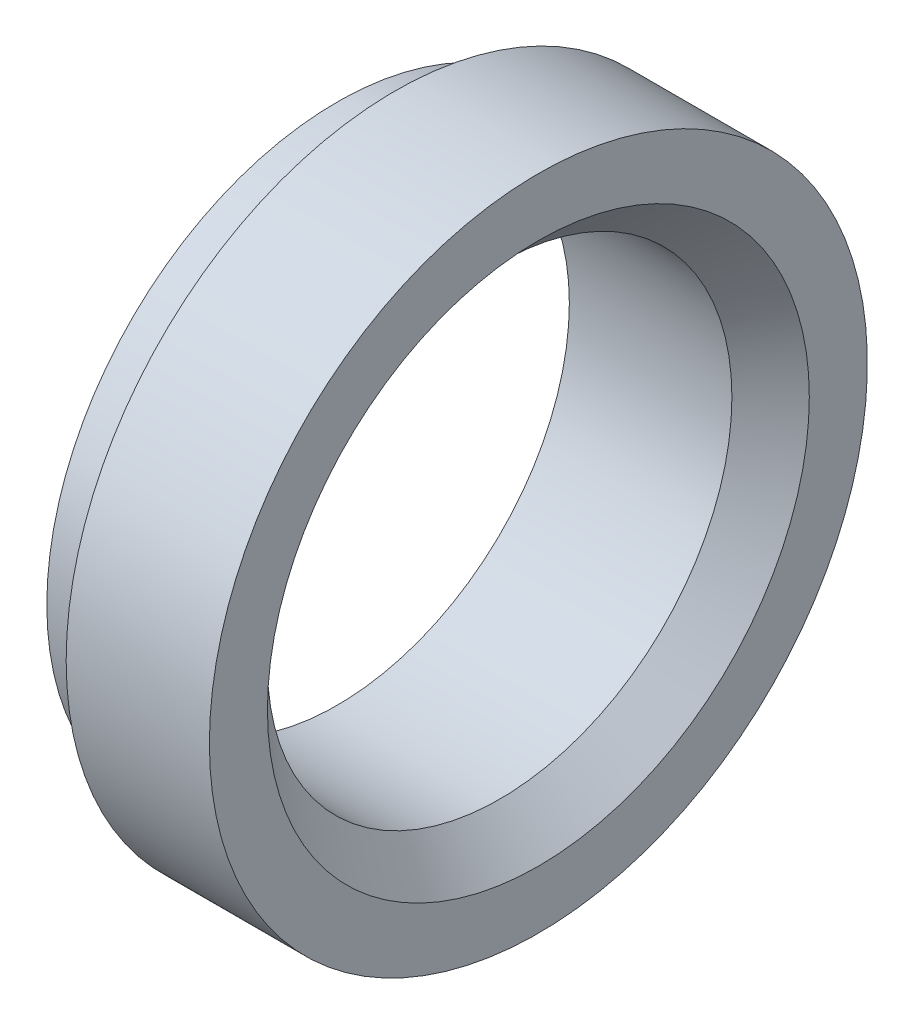
SolidWorks part; units mm, degrees
ref_plane "Front" through (0, 0, 0) normal (0, 0, 1) x (1, 0, 0)
ref_plane "Top" through (0, 0, 0) normal (0, 1, 0) x (1, 0, 0)
ref_plane "Right" through (0, 0, 0) normal (1, 0, 0) x (0, 0, -1)
sketch "Sketch1" plane through (0, 0, 0) normal (0, 0, 1) x (1, 0, 0)
  line L0 (0, 6) -> (0, 7.5)
  line L1 (0, 7.5) -> (1.5, 7.5)
  line L2 (1.5, 7.5) -> (1.5, 8.5)
  line L3 (1.5, 8.5) -> (5.2, 8.5)
  line L4 (5.2, 8.5) -> (5.2, 8.5323)
  line L5 (5.2, 8.5) -> (5.2, 7)
  line L6 (4.2, 6) -> (0, 6)
  line L7 (4.2, 6) -> (5.2, 7)
  line L8 (0, 0) -> (8.5219, 0) construction
  dimension "D1" = 1.5
  dimension "D2" = 1
  dimension "D3" = 1.5
  dimension "D4" = 3.7
  dimension "D5" = 4.2
  dimension "D6" = 45
  dimension "D7" = 6
  dimension "D8" = 7.5
  dimension "D9" = 8.5
revolve "Revolve4" add sketch "Sketch1" angle 360 about L8
